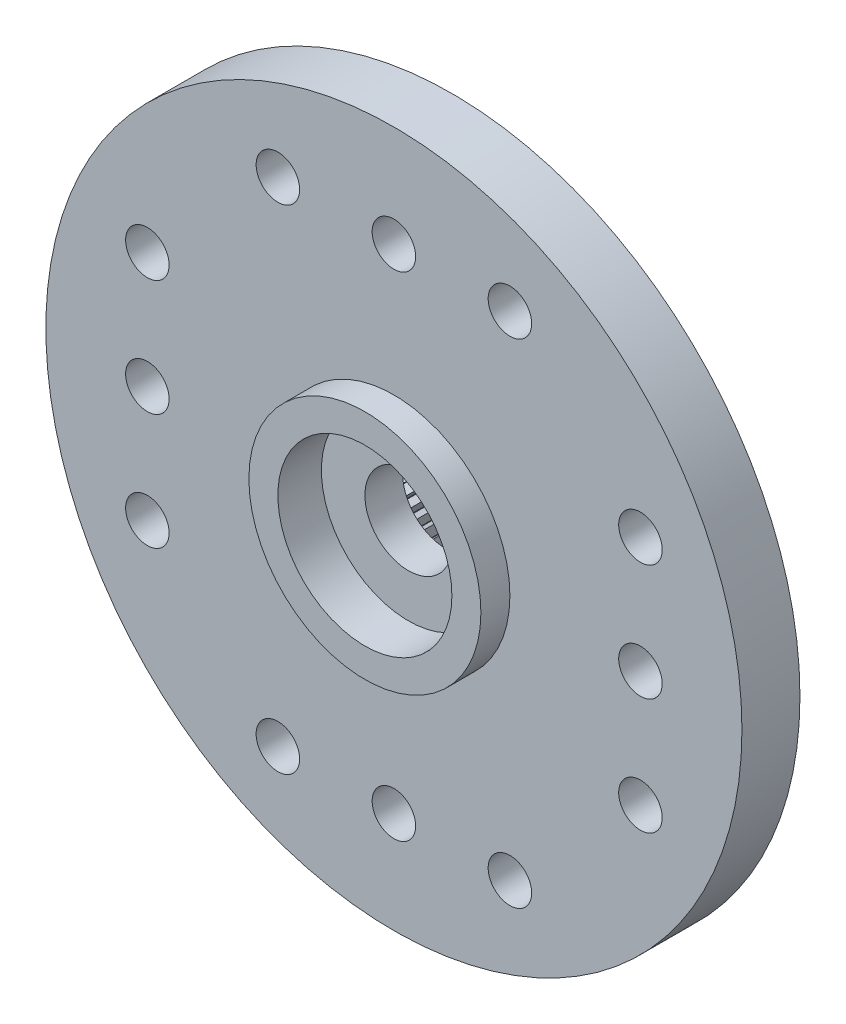
SolidWorks part; units mm, degrees
material "PE haute densité"
ref_plane "Plan de face" through (0, 0, 0) normal (0, 0, 1) x (1, 0, 0)
ref_plane "Plan de dessus" through (0, 0, 0) normal (0, 1, 0) x (1, 0, 0)
ref_plane "Plan de droite" through (0, 0, 0) normal (1, 0, 0) x (0, 0, -1)
sketch "Esquisse1" plane through (0, 0, 0) normal (0, 0, 1) x (1, 0, 0)
  circle A0 centre (0, 0) radius 4.5
extrude "Boss.-Extru.1" add sketch "Esquisse1" along normal blind 3.5
sketch "Esquisse2" plane through (0, 0, 3.5) normal (0, 0, 1) x (1, 0, 0)
  circle A0 centre (0, 0) radius 12
extrude "Boss.-Extru.2" add sketch "Esquisse2" along normal blind 2
sketch "Esquisse5" plane through (0, 0, 5.5) normal (0, 0, 1) x (1, 0, 0)
  circle A0 centre (0, 0) radius 4
extrude "Boss.-Extru.3" add sketch "Esquisse5" along normal blind 1
hole_wizard "Diamètre du perçage Ø3.0 (3)2" positions "Esquisse7" profile "Esquisse6" hole size "Ø3.0" standard "ISO" end condition through all
sketch "Esquisse7" plane through (0, 0, 6.5) normal (0, 0, 1) x (1, 0, 0)
  point P0 (0, 0)
sketch "Esquisse6" plane through (0, 0, 6.5) normal (1, 0, 0) x (0, -1, 0)
  line L0 (0, 0) -> (0, 6.5)
  line L1 (0, 6.5) -> (1.5, 6.5)
  line L2 (1.5, 6.5) -> (1.5, 0)
  line L5 (1.5, 0) -> (0, 0)
  line L11 (0, -6.35) -> (0, 107.95) construction
  dimension "Diamètre du perçage jusqu'au prochain" = 3
  dimension "Profondeur du perçage jusqu'au prochain" = 6.5
sketch "Esquisse8" plane through (0, 0, 6.5) normal (0, 0, 1) x (1, 0, 0)
  circle A0 centre (0, 0) radius 3
extrude "Enlèv. mat.-Extru.1" cut sketch "Esquisse8" against normal blind 1.5
sketch "Esquisse9" plane through (0, 0, 0) normal (0, 0, -1) x (-1, 0, 0)
  line L0 (0, 2.5) -> (0.18, 2.9946)
  line L1 (0, 2.5) -> (1.137, 2.5) construction
  line L2 (0, 2.5) -> (-0.18, 2.9946)
  line L3 (0.3133, 2.4803) -> (0.1967, 2.9935)
  line L4 (0.3133, 2.4803) -> (0.5539, 2.9484)
  line L5 (0.6217, 2.4215) -> (0.5704, 2.9453)
  line L6 (0.6217, 2.4215) -> (0.9191, 2.8557)
  line L7 (0.9203, 2.3244) -> (0.935, 2.8506)
  line L8 (0.9203, 2.3244) -> (1.2698, 2.718)
  line L9 (1.2044, 2.1908) -> (1.2849, 2.7109)
  line L10 (1.2044, 2.1908) -> (1.6004, 2.5375)
  line L11 (1.4695, 2.0225) -> (1.6145, 2.5285)
  line L12 (1.4695, 2.0225) -> (1.9058, 2.3169)
  line L13 (1.7114, 1.8224) -> (1.9187, 2.3062)
  line L14 (1.7114, 1.8224) -> (2.1812, 2.0597)
  line L15 (1.9263, 1.5936) -> (2.1926, 2.0475)
  line L16 (1.9263, 1.5936) -> (2.4221, 1.7701)
  line L17 (2.1108, 1.3396) -> (2.432, 1.7566)
  line L18 (2.1108, 1.3396) -> (2.6249, 1.4526)
  line L19 (2.2621, 1.0644) -> (2.6329, 1.4379)
  line L20 (2.2621, 1.0644) -> (2.7862, 1.1122)
  line L21 (2.3776, 0.7725) -> (2.7924, 1.0966)
  line L22 (2.3776, 0.7725) -> (2.9037, 0.7542)
  line L23 (2.4557, 0.4685) -> (2.9078, 0.738)
  line L24 (2.4557, 0.4685) -> (2.9753, 0.3843)
  line L25 (2.4951, 0.157) -> (2.9774, 0.3677)
  line L26 (2.4951, 0.157) -> (3, 0.0084)
  line L27 (2.4951, -0.157) -> (3, -0.0084)
  line L28 (2.4951, -0.157) -> (2.9774, -0.3677)
  line L29 (2.4557, -0.4685) -> (2.9753, -0.3843)
  line L30 (2.4557, -0.4685) -> (2.9078, -0.738)
  line L31 (2.3776, -0.7725) -> (2.9037, -0.7542)
  line L32 (2.3776, -0.7725) -> (2.7924, -1.0966)
  line L33 (2.2621, -1.0644) -> (2.7862, -1.1122)
  line L34 (2.2621, -1.0644) -> (2.6329, -1.4379)
  line L35 (2.1108, -1.3396) -> (2.6249, -1.4526)
  line L36 (2.1108, -1.3396) -> (2.432, -1.7566)
  line L37 (1.9263, -1.5936) -> (2.4221, -1.7701)
  line L38 (1.9263, -1.5936) -> (2.1926, -2.0475)
  line L39 (1.7114, -1.8224) -> (2.1812, -2.0597)
  line L40 (1.7114, -1.8224) -> (1.9187, -2.3062)
  line L41 (1.4695, -2.0225) -> (1.9058, -2.3169)
  line L42 (1.4695, -2.0225) -> (1.6145, -2.5285)
  line L43 (1.2044, -2.1908) -> (1.6004, -2.5375)
  line L44 (1.2044, -2.1908) -> (1.2849, -2.7109)
  line L45 (0.9203, -2.3244) -> (1.2698, -2.718)
  line L46 (0.9203, -2.3244) -> (0.935, -2.8506)
  line L47 (0.6217, -2.4215) -> (0.9191, -2.8557)
  line L48 (0.6217, -2.4215) -> (0.5704, -2.9453)
  line L49 (0.3133, -2.4803) -> (0.5539, -2.9484)
  line L50 (0.3133, -2.4803) -> (0.1967, -2.9935)
  line L51 (0, -2.5) -> (0.18, -2.9946)
  line L52 (0, -2.5) -> (-0.18, -2.9946)
  line L53 (-0.3133, -2.4803) -> (-0.1967, -2.9935)
  line L54 (-0.3133, -2.4803) -> (-0.5539, -2.9484)
  line L55 (-0.6217, -2.4215) -> (-0.5704, -2.9453)
  line L56 (-0.6217, -2.4215) -> (-0.9191, -2.8557)
  line L57 (-0.9203, -2.3244) -> (-0.935, -2.8506)
  line L58 (-0.9203, -2.3244) -> (-1.2698, -2.718)
  line L59 (-1.2044, -2.1908) -> (-1.2849, -2.7109)
  line L60 (-1.2044, -2.1908) -> (-1.6004, -2.5375)
  line L61 (-1.4695, -2.0225) -> (-1.6145, -2.5285)
  line L62 (-1.4695, -2.0225) -> (-1.9058, -2.3169)
  line L63 (-1.7114, -1.8224) -> (-1.9187, -2.3062)
  line L64 (-1.7114, -1.8224) -> (-2.1812, -2.0597)
  line L65 (-1.9263, -1.5936) -> (-2.1926, -2.0475)
  line L66 (-1.9263, -1.5936) -> (-2.4221, -1.7701)
  line L67 (-2.1108, -1.3396) -> (-2.432, -1.7566)
  line L68 (-2.1108, -1.3396) -> (-2.6249, -1.4526)
  line L69 (-2.2621, -1.0644) -> (-2.6329, -1.4379)
  line L70 (-2.2621, -1.0644) -> (-2.7862, -1.1122)
  line L71 (-2.3776, -0.7725) -> (-2.7924, -1.0966)
  line L72 (-2.3776, -0.7725) -> (-2.9037, -0.7542)
  line L73 (-2.4557, -0.4685) -> (-2.9078, -0.738)
  line L74 (-2.4557, -0.4685) -> (-2.9753, -0.3843)
  line L75 (-2.4951, -0.157) -> (-2.9774, -0.3677)
  line L76 (-2.4951, -0.157) -> (-3, -0.0084)
  line L77 (-2.4951, 0.157) -> (-3, 0.0084)
  line L78 (-2.4951, 0.157) -> (-2.9774, 0.3677)
  line L79 (-2.4557, 0.4685) -> (-2.9753, 0.3843)
  line L80 (-2.4557, 0.4685) -> (-2.9078, 0.738)
  line L81 (-2.3776, 0.7725) -> (-2.9037, 0.7542)
  line L82 (-2.3776, 0.7725) -> (-2.7924, 1.0966)
  line L83 (-2.2621, 1.0644) -> (-2.7862, 1.1122)
  line L84 (-2.2621, 1.0644) -> (-2.6329, 1.4379)
  line L85 (-2.1108, 1.3396) -> (-2.6249, 1.4526)
  line L86 (-2.1108, 1.3396) -> (-2.432, 1.7566)
  line L87 (-1.9263, 1.5936) -> (-2.4221, 1.7701)
  line L88 (-1.9263, 1.5936) -> (-2.1926, 2.0475)
  line L89 (-1.7114, 1.8224) -> (-2.1812, 2.0597)
  line L90 (-1.7114, 1.8224) -> (-1.9187, 2.3062)
  line L91 (-1.4695, 2.0225) -> (-1.9058, 2.3169)
  line L92 (-1.4695, 2.0225) -> (-1.6145, 2.5285)
  line L93 (-1.2044, 2.1908) -> (-1.6004, 2.5375)
  line L94 (-1.2044, 2.1908) -> (-1.2849, 2.7109)
  line L95 (-0.9203, 2.3244) -> (-1.2698, 2.718)
  line L96 (-0.9203, 2.3244) -> (-0.935, 2.8506)
  line L97 (-0.6217, 2.4215) -> (-0.9191, 2.8557)
  line L98 (-0.6217, 2.4215) -> (-0.5704, 2.9453)
  line L99 (-0.3133, 2.4803) -> (-0.5539, 2.9484)
  line L100 (-0.3133, 2.4803) -> (-0.1967, 2.9935)
  arc A0 (0.1967, 2.9935) -> (0.18, 2.9946) centre (0, 0) ccw
  circle A1 centre (0, 0) radius 2.5 construction
  arc A2 (0.5704, 2.9453) -> (0.5539, 2.9484) centre (0, 0) ccw
  arc A3 (0.935, 2.8506) -> (0.9191, 2.8557) centre (0, 0) ccw
  arc A4 (1.2849, 2.7109) -> (1.2698, 2.718) centre (0, 0) ccw
  arc A5 (1.6145, 2.5285) -> (1.6004, 2.5375) centre (0, 0) ccw
  arc A6 (1.9187, 2.3062) -> (1.9058, 2.3169) centre (0, 0) ccw
  arc A7 (2.1926, 2.0475) -> (2.1812, 2.0597) centre (0, 0) ccw
  arc A8 (2.432, 1.7566) -> (2.4221, 1.7701) centre (0, 0) ccw
  arc A9 (2.6329, 1.4379) -> (2.6249, 1.4526) centre (0, 0) ccw
  arc A10 (2.7924, 1.0966) -> (2.7862, 1.1122) centre (0, 0) ccw
  arc A11 (2.9078, 0.738) -> (2.9037, 0.7542) centre (0, 0) ccw
  arc A12 (2.9774, 0.3677) -> (2.9753, 0.3843) centre (0, 0) ccw
  arc A13 (3, -0.0084) -> (3, 0.0084) centre (0, 0) ccw
  arc A14 (2.9753, -0.3843) -> (2.9774, -0.3677) centre (0, 0) ccw
  arc A15 (2.9037, -0.7542) -> (2.9078, -0.738) centre (0, 0) ccw
  arc A16 (2.7862, -1.1122) -> (2.7924, -1.0966) centre (0, 0) ccw
  arc A17 (2.6249, -1.4526) -> (2.6329, -1.4379) centre (0, 0) ccw
  arc A18 (2.4221, -1.7701) -> (2.432, -1.7566) centre (0, 0) ccw
  arc A19 (2.1812, -2.0597) -> (2.1926, -2.0475) centre (0, 0) ccw
  arc A20 (1.9058, -2.3169) -> (1.9187, -2.3062) centre (0, 0) ccw
  arc A21 (1.6004, -2.5375) -> (1.6145, -2.5285) centre (0, 0) ccw
  arc A22 (1.2698, -2.718) -> (1.2849, -2.7109) centre (0, 0) ccw
  arc A23 (0.9191, -2.8557) -> (0.935, -2.8506) centre (0, 0) ccw
  arc A24 (0.5539, -2.9484) -> (0.5704, -2.9453) centre (0, 0) ccw
  arc A25 (0.18, -2.9946) -> (0.1967, -2.9935) centre (0, 0) ccw
  arc A26 (-0.1967, -2.9935) -> (-0.18, -2.9946) centre (0, 0) ccw
  arc A27 (-0.5704, -2.9453) -> (-0.5539, -2.9484) centre (0, 0) ccw
  arc A28 (-0.935, -2.8506) -> (-0.9191, -2.8557) centre (0, 0) ccw
  arc A29 (-1.2849, -2.7109) -> (-1.2698, -2.718) centre (0, 0) ccw
  arc A30 (-1.6145, -2.5285) -> (-1.6004, -2.5375) centre (0, 0) ccw
  arc A31 (-1.9187, -2.3062) -> (-1.9058, -2.3169) centre (0, 0) ccw
  arc A32 (-2.1926, -2.0475) -> (-2.1812, -2.0597) centre (0, 0) ccw
  arc A33 (-2.432, -1.7566) -> (-2.4221, -1.7701) centre (0, 0) ccw
  arc A34 (-2.6329, -1.4379) -> (-2.6249, -1.4526) centre (0, 0) ccw
  arc A35 (-2.7924, -1.0966) -> (-2.7862, -1.1122) centre (0, 0) ccw
  arc A36 (-2.9078, -0.738) -> (-2.9037, -0.7542) centre (0, 0) ccw
  arc A37 (-2.9774, -0.3677) -> (-2.9753, -0.3843) centre (0, 0) ccw
  arc A38 (-3, 0.0084) -> (-3, -0.0084) centre (0, 0) ccw
  arc A39 (-2.9753, 0.3843) -> (-2.9774, 0.3677) centre (0, 0) ccw
  arc A40 (-2.9037, 0.7542) -> (-2.9078, 0.738) centre (0, 0) ccw
  arc A41 (-2.7862, 1.1122) -> (-2.7924, 1.0966) centre (0, 0) ccw
  arc A42 (-2.6249, 1.4526) -> (-2.6329, 1.4379) centre (0, 0) ccw
  arc A43 (-2.4221, 1.7701) -> (-2.432, 1.7566) centre (0, 0) ccw
  arc A44 (-2.1812, 2.0597) -> (-2.1926, 2.0475) centre (0, 0) ccw
  arc A45 (-1.9058, 2.3169) -> (-1.9187, 2.3062) centre (0, 0) ccw
  arc A46 (-1.6004, 2.5375) -> (-1.6145, 2.5285) centre (0, 0) ccw
  arc A47 (-1.2698, 2.718) -> (-1.2849, 2.7109) centre (0, 0) ccw
  arc A48 (-0.9191, 2.8557) -> (-0.935, 2.8506) centre (0, 0) ccw
  arc A49 (-0.5539, 2.9484) -> (-0.5704, 2.9453) centre (0, 0) ccw
  arc A50 (-0.18, 2.9946) -> (-0.1967, 2.9935) centre (0, 0) ccw
  point P157 (0, 0)
  point P256 (0, 0)
  dimension "D1" = 70
  dimension "D2" = 6
  dimension "D3" = 5
  dimension "D4" = 110
  dimension "D5" = 50
  dimension "D6" = 50
extrude "Enlèv. mat.-Extru.2" cut sketch "Esquisse9" against normal blind 3.7
hole_wizard "Diamètre du perçage Ø1.5 (1.5)1" positions "Esquisse11" profile "Esquisse10" hole size "Ø1.5" standard "ISO" end condition through all
sketch "Esquisse11" plane through (0, 0, 5.5) normal (0, 0, 1) x (1, 0, 0)
  point P0 (-8.5, 0)
  point P2 (-8.5, 4)
  point P4 (-8.5, -4)
  dimension "D1" = 8.5
  dimension "D2" = 4
  dimension "D3" = 4
sketch "Esquisse10" plane through (-8.5, 0, 5.5) normal (1, 0, 0) x (0, -1, 0)
  line L0 (0, 0) -> (0, 5.5)
  line L1 (0, 5.5) -> (0.75, 5.5)
  line L2 (0.75, 5.5) -> (0.75, 0)
  line L5 (0.75, 0) -> (0, 0)
  line L11 (0, -6.35) -> (0, 107.95) construction
  dimension "Diamètre du perçage jusqu'au prochain" = 1.5
  dimension "Profondeur du perçage jusqu'au prochain" = 5.5
pattern_circular "Répétition circulaire1" count 4 over 360 about axis through (0, 0, 0) along (0, 0, 1) of "Diamètre du perçage Ø1.5 (1.5)1"
